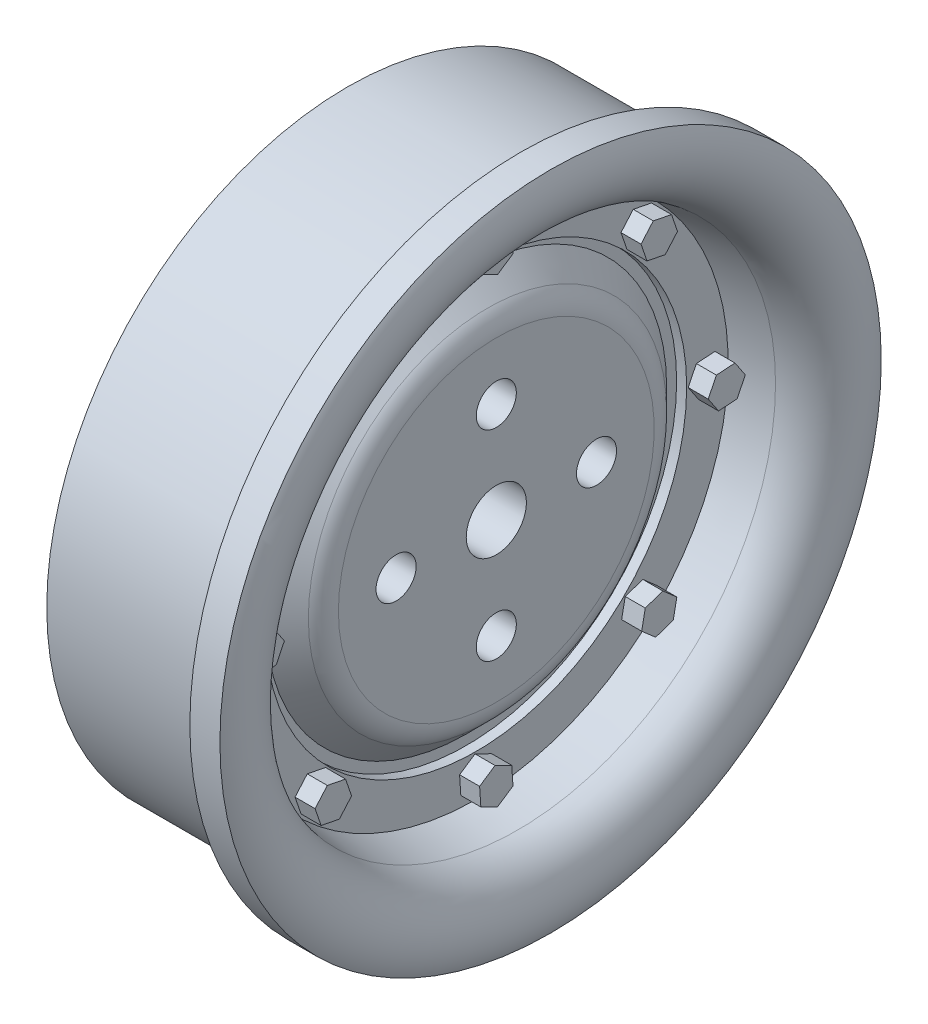
SolidWorks part; units mm, degrees
ref_plane "Front Plane" through (0, 0, 0) normal (0, 0, 1) x (1, 0, 0)
ref_plane "Top Plane" through (0, 0, 0) normal (0, 1, 0) x (1, 0, 0)
ref_plane "Right Plane" through (0, 0, 0) normal (1, 0, 0) x (0, 0, -1)
sketch "Sketch1" plane through (0, 0, 0) normal (0, 1, 0) x (1, 0, 0)
  line L0 (-25, 0) -> (25, 0) construction
  line L1 (0, 77.8341) -> (0, -61.2926) construction
  line L20 (0.0954, 16.5) -> (-1.4046, 16.5)
  line L21 (-1.4046, 16.5) -> (-1.4046, 15)
  line L22 (-1.4046, 15) -> (-10.0446, 15)
  line L29 (-1.5431, 12.8638) -> (-3.6131, 12.5708)
  line L30 (-4.1131, 10.5) -> (-4.1131, 10)
  line L31 (-4.1131, 10) -> (-2.6131, 8.5)
  line L32 (-2.6131, 8.5) -> (-2.6131, 1.5)
  line L33 (-10.0446, 15) -> (-10.0446, 13)
  line L34 (-10.0446, 13) -> (-7.6315, 13)
  line L35 (-7.6315, 13) -> (-7.6315, 3.5)
  line L36 (-7.6315, 3.5) -> (-10.0446, 3.5)
  line L37 (-10.0446, 3.5) -> (-10.0446, 1.5)
  line L38 (-10.0446, 1.5) -> (-7.6315, 1.5)
  line L40 (-4.1131, 10.5) -> (-3.6131, 10.5)
  line L41 (-3.6131, 10.5) -> (-3.6131, 12.5708)
  line L42 (-7.6315, 1.5) -> (-2.6131, 1.5)
  arc A0 (0.0954, 16.5) -> (-1.5431, 12.8638) centre (-2.1397, 15.3198) cw
  dimension "D1" = 50
  dimension "D2" = 25
  dimension "D3" = 25
  dimension "D4" = 33
  dimension "D5" = 30
  dimension "D6" = 1.5
  dimension "D7" = 1.5
  dimension "D8" = 8.64
  dimension "D9" = 1
  dimension "D10" = 2
  dimension "D11" = 3
  dimension "D13" = 2
  dimension "D14" = 0.5
  dimension "D15" = 0.5
revolve "Revolve1" add sketch "Sketch1" angle 360 about L0
fillet "Fillet1" radius 1.5 1 edges at (-2.6131, 0, 8.5)
sketch "Sketch2" plane through (-2.6131, 0, 0) normal (1, 0, 0) x (0, 0, -1)
  circle A0 centre (0, 0) radius 5 construction
  circle A1 centre (0, 5) radius 1
  circle A2 centre (5, 0) radius 1
  circle A3 centre (0, -5) radius 1
  circle A4 centre (-5, 0) radius 1
  point P14 (0, 0)
  dimension "D1" = 10
  dimension "D2" = 2
  dimension "D3" = 4
extrude "Cut-Extrude1" cut sketch "Sketch2" against normal mid plane 10
sketch "Sketch3" plane through (-3.6131, 0, 0) normal (1, 0, 0) x (0, 0, -1)
  line L0 (8.4309, 7.2538) -> (9.0416, 7.9519)
  line L1 (0.8323, 11.0908) -> (0.7706, 12.0162)
  line L2 (0.7706, 12.0162) -> (-0.0618, 12.4254)
  line L3 (-0.0618, 12.4254) -> (-0.8323, 11.9092)
  line L4 (-0.8323, 11.9092) -> (-0.7706, 10.9838)
  line L5 (-0.7706, 10.9838) -> (0.0618, 10.5746)
  line L6 (0.0618, 10.5746) -> (0.8323, 11.0908)
  line L7 (9.0416, 7.9519) -> (8.7424, 8.8298)
  line L8 (8.7424, 8.8298) -> (7.8325, 9.0096)
  line L9 (7.8325, 9.0096) -> (7.2218, 8.3116)
  line L10 (7.2218, 8.3116) -> (7.521, 7.4337)
  line L11 (7.521, 7.4337) -> (8.4309, 7.2538)
  line L12 (11.0908, -0.8323) -> (12.0162, -0.7706)
  line L13 (12.0162, -0.7706) -> (12.4254, 0.0618)
  line L14 (12.4254, 0.0618) -> (11.9092, 0.8323)
  line L15 (11.9092, 0.8323) -> (10.9838, 0.7706)
  line L16 (10.9838, 0.7706) -> (10.5746, -0.0618)
  line L17 (10.5746, -0.0618) -> (11.0908, -0.8323)
  line L18 (7.2538, -8.4309) -> (7.9519, -9.0416)
  line L19 (7.9519, -9.0416) -> (8.8298, -8.7424)
  line L20 (8.8298, -8.7424) -> (9.0096, -7.8325)
  line L21 (9.0096, -7.8325) -> (8.3116, -7.2218)
  line L22 (8.3116, -7.2218) -> (7.4337, -7.521)
  line L23 (7.4337, -7.521) -> (7.2538, -8.4309)
  line L24 (-0.8323, -11.0908) -> (-0.7706, -12.0162)
  line L25 (-0.7706, -12.0162) -> (0.0618, -12.4254)
  line L26 (0.0618, -12.4254) -> (0.8323, -11.9092)
  line L27 (0.8323, -11.9092) -> (0.7706, -10.9838)
  line L28 (0.7706, -10.9838) -> (-0.0618, -10.5746)
  line L29 (-0.0618, -10.5746) -> (-0.8323, -11.0908)
  line L30 (-8.4309, -7.2538) -> (-9.0416, -7.9519)
  line L31 (-9.0416, -7.9519) -> (-8.7424, -8.8298)
  line L32 (-8.7424, -8.8298) -> (-7.8325, -9.0096)
  line L33 (-7.8325, -9.0096) -> (-7.2218, -8.3116)
  line L34 (-7.2218, -8.3116) -> (-7.521, -7.4337)
  line L35 (-7.521, -7.4337) -> (-8.4309, -7.2538)
  line L36 (-11.0908, 0.8323) -> (-12.0162, 0.7706)
  line L37 (-12.0162, 0.7706) -> (-12.4254, -0.0618)
  line L38 (-12.4254, -0.0618) -> (-11.9092, -0.8323)
  line L39 (-11.9092, -0.8323) -> (-10.9838, -0.7706)
  line L40 (-10.9838, -0.7706) -> (-10.5746, 0.0618)
  line L41 (-10.5746, 0.0618) -> (-11.0908, 0.8323)
  line L42 (-7.2538, 8.4309) -> (-7.9519, 9.0416)
  line L43 (-7.9519, 9.0416) -> (-8.8298, 8.7424)
  line L44 (-8.8298, 8.7424) -> (-9.0096, 7.8325)
  line L45 (-9.0096, 7.8325) -> (-8.3116, 7.2218)
  line L46 (-8.3116, 7.2218) -> (-7.4337, 7.521)
  line L47 (-7.4337, 7.521) -> (-7.2538, 8.4309)
  circle A0 centre (0, 0) radius 11.5 construction
  circle A9 centre (0, 11.5) radius 0.8032 construction
  point P22 (0, 0)
  point P57 (0, 0)
  dimension "D1" = 23
  dimension "D2" = 8
extrude "Boss-Extrude1" add sketch "Sketch3" along normal blind 1
